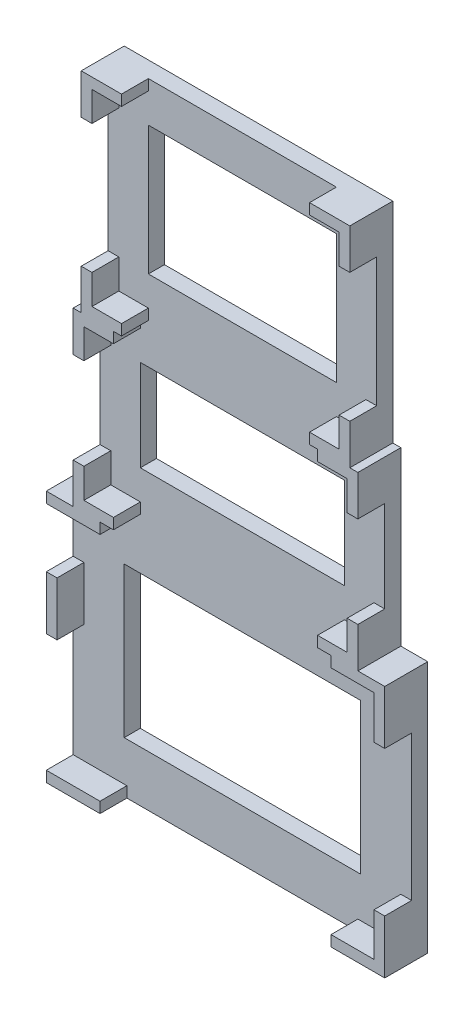
SolidWorks part; units mm, degrees
ref_plane "Front Plane" through (0, 0, 0) normal (0, 0, 1) x (1, 0, 0)
ref_plane "Top Plane" through (0, 0, 0) normal (0, 1, 0) x (1, 0, 0)
ref_plane "Right Plane" through (0, 0, 0) normal (1, 0, 0) x (0, 0, -1)
sketch "Sketch1" plane through (0, 0, 0) normal (0, 0, 1) x (1, 0, 0)
  line L0 (0, 47) -> (5, 47)
  line L1 (0, 0) -> (63, 0)
  line L2 (0, 0) -> (0, 47)
  line L3 (0, 47) -> (63, 47)
  line L4 (63, 0) -> (63, 47)
  line L5 (63, 47) -> (58, 47)
  line L6 (5, 79) -> (6.5, 79)
  line L7 (5, 47) -> (58, 47)
  line L8 (5, 47) -> (5, 79)
  line L9 (5, 79) -> (58, 79)
  line L10 (58, 47) -> (58, 79)
  line L11 (58, 79) -> (56.5, 79)
  line L13 (6.5, 79) -> (56.5, 79)
  line L14 (6.5, 79) -> (6.5, 118)
  line L15 (6.5, 118) -> (56.5, 118)
  line L16 (56.5, 79) -> (56.5, 118)
  dimension "D1" = 63
  dimension "D2" = 47
  dimension "D3" = 5
  dimension "D4" = 5
  dimension "D5" = 32
  dimension "D6" = 1.5
  dimension "D7" = 1.5
  dimension "D8" = 39
extrude "Boss-Extrude1" add sketch "Sketch1" along normal blind 3 contours L1 L4 L3 L0 L2 | L3 L10 L9 L6 L8 | L9 L16 L15 L14
sketch "Sketch2" plane through (0, 0, 3) normal (0, 0, 1) x (1, 0, 0)
  line L0 (0, 47) -> (0, 34)
  line L1 (0, 0) -> (0, 47) construction
  line L2 (0, 34) -> (0, 24)
  line L3 (0, 24) -> (2, 24)
  line L4 (2, 24) -> (2, 34)
  line L5 (2, 34) -> (0, 34)
  line L7 (0, 47) -> (10, 47)
  line L8 (0, 47) -> (0, 45)
  line L9 (0, 45) -> (10, 45)
  line L10 (10, 47) -> (10, 45)
  line L11 (0, 0) -> (10, 0)
  line L12 (0, 0) -> (0, 2)
  line L13 (0, 2) -> (10, 2)
  line L14 (10, 0) -> (10, 2)
  line L15 (63, 0) -> (53, 0)
  line L16 (63, 0) -> (63, 2)
  line L17 (63, 2) -> (53, 2)
  line L18 (53, 0) -> (53, 2)
  line L19 (63, 0) -> (61, 0)
  line L20 (63, 0) -> (63, 10)
  line L21 (63, 10) -> (61, 10)
  line L22 (61, 0) -> (61, 10)
  line L23 (63, 47) -> (53, 47)
  line L24 (63, 47) -> (63, 45)
  line L25 (63, 45) -> (53, 45)
  line L26 (53, 47) -> (53, 45)
  line L27 (63, 47) -> (61, 47)
  line L28 (63, 47) -> (63, 37)
  line L29 (63, 37) -> (61, 37)
  line L30 (61, 47) -> (61, 37)
  line M6 (0, 0) -> (63, 0)
  line M7 (63, 0) -> (63, 47)
  line M8 (63, 47) -> (58, 47)
  line M17 (0, 47) -> (0, 0)
  dimension "D1" = 13
  dimension "D2" = 10
  dimension "D3" = 2
  dimension "D4" = 10
  dimension "D5" = 2
  dimension "D6" = 10
  dimension "D7" = 2
  dimension "D8" = 10
  dimension "D9" = 10
  dimension "D10" = 2
  dimension "D11" = 2
  dimension "D12" = 10
  dimension "D13" = 2
  dimension "D14" = 2
  dimension "D15" = 10
extrude "Boss-Extrude2" add sketch "Sketch2" along normal blind 5 contours L30 L23 L26 L25 | L30 L25 M8 M7 | L25 L30 L29 M7 | L22 L17 L21 M7 | L22 L15 L17 M7 | L22 L17 L18 M6 | L14 L13 M6 M17 | L7 L10 L9 L8 | L2 L3 L4 L5
sketch "Sketch3" plane through (0, 0, 3) normal (0, 0, 1) x (1, 0, 0)
  line L0 (9.5, 45) -> (9.5, 37.5)
  line L1 (10, 2) -> (10, 9.5)
  line L2 (61, 37) -> (53.5, 37)
  line L3 (2, 24) -> (9.5, 24)
  line L4 (0, 45) -> (10, 45) construction
  line L6 (9.5, 37.5) -> (53.5, 37.5)
  line L7 (9.5, 37.5) -> (9.5, 9.5)
  line L8 (9.5, 9.5) -> (53.5, 9.5)
  line L9 (53.5, 37.5) -> (53.5, 9.5)
  dimension "D1" = 7.5
  dimension "D2" = 7.5
  dimension "D3" = 7.5
  dimension "D4" = 7.5
extrude "Cut-Extrude1" cut sketch "Sketch3" against normal blind 5 contours L9 L6 L7 L8
sketch "Sketch4" plane through (0, 0, 3) normal (0, 0, 1) x (1, 0, 0)
  line L0 (63, 47) -> (53, 47) construction
  line L1 (5, 47) -> (12.5, 47)
  line L2 (5, 47) -> (5, 49)
  line L3 (5, 49) -> (12.5, 49)
  line L4 (12.5, 47) -> (12.5, 49)
  line L5 (5, 47) -> (7, 47)
  line L6 (5, 47) -> (5, 54.5)
  line L7 (5, 54.5) -> (7, 54.5)
  line L8 (7, 47) -> (7, 54.5)
  line L9 (58, 47) -> (50.5, 47)
  line L10 (58, 47) -> (58, 49)
  line L11 (58, 49) -> (50.5, 49)
  line L12 (50.5, 47) -> (50.5, 49)
  line L14 (58, 47) -> (56, 47)
  line L15 (58, 47) -> (58, 54.5)
  line L16 (58, 54.5) -> (56, 54.5)
  line L17 (56, 47) -> (56, 54.5)
  line L18 (58, 79) -> (56, 79)
  line L19 (58, 79) -> (58, 71.5)
  line L20 (58, 71.5) -> (56, 71.5)
  line L21 (56, 79) -> (56, 71.5)
  line L22 (58, 79) -> (50.5, 79)
  line L23 (58, 79) -> (58, 77)
  line L24 (58, 77) -> (50.5, 77)
  line L25 (50.5, 79) -> (50.5, 77)
  line L26 (5, 79) -> (12.5, 79)
  line L27 (5, 79) -> (5, 77)
  line L28 (5, 77) -> (12.5, 77)
  line L29 (12.5, 79) -> (12.5, 77)
  line L30 (5, 79) -> (7, 79)
  line L31 (5, 79) -> (5, 71.5)
  line L32 (5, 71.5) -> (7, 71.5)
  line L33 (7, 79) -> (7, 71.5)
  line M20 (53, 47) -> (58, 47)
  line M21 (58, 47) -> (58, 79)
  line M22 (58, 79) -> (56.5, 79)
  line M26 (6.5, 79) -> (5, 79)
  line M27 (5, 79) -> (5, 47)
  line M28 (5, 47) -> (10, 47)
  dimension "D1" = 7.5
  dimension "D2" = 2
  dimension "D3" = 7.5
  dimension "D4" = 2
  dimension "D5" = 2
  dimension "D6" = 7.5
  dimension "D7" = 2
  dimension "D8" = 7.5
  dimension "D9" = 2
  dimension "D10" = 7.5
  dimension "D11" = 2
  dimension "D12" = 7.5
  dimension "D13" = 2
  dimension "D14" = 2
  dimension "D15" = 7.5
  dimension "D16" = 7.5
extrude "Boss-Extrude3" add sketch "Sketch4" along normal blind 5 contours L8 L3 M28 M27 | L3 L8 L7 M27 | L8 L1 L4 L3 | L33 L28 L32 M27 | L33 L26 L28 M26 M27 | L26 L33 L28 L29 | L22 L25 L24 L21 | L24 L19 L18 L21 M22 | L24 L21 L20 M21 | L17 L11 L16 M21 | L17 L9 L11 M21 | L17 L11 L12 L9 M20
sketch "Sketch5" plane through (0, 0, 3) normal (0, 0, 1) x (1, 0, 0)
  line L1 (6.5, 79) -> (14, 79)
  line L2 (6.5, 79) -> (6.5, 81)
  line L3 (6.5, 81) -> (14, 81)
  line L4 (14, 79) -> (14, 81)
  line L5 (6.5, 79) -> (8.5, 79)
  line L6 (6.5, 79) -> (6.5, 86.5)
  line L7 (6.5, 86.5) -> (8.5, 86.5)
  line L8 (8.5, 79) -> (8.5, 86.5)
  line L9 (56.5, 79) -> (49, 79)
  line L10 (56.5, 79) -> (56.5, 81)
  line L11 (56.5, 81) -> (49, 81)
  line L12 (49, 79) -> (49, 81)
  line L13 (56.5, 79) -> (56.5175, 79)
  line L14 (56.5, 79) -> (56.5, 86.5)
  line L17 (56.5, 79) -> (54.5, 79)
  line L18 (56.5, 79) -> (56.5, 86.5)
  line L19 (56.5, 86.5) -> (54.5, 86.5)
  line L20 (54.5, 79) -> (54.5, 86.5)
  line L22 (6.5, 118) -> (8.5, 118)
  line L23 (6.5, 118) -> (6.5, 110.5)
  line L24 (6.5, 110.5) -> (8.5, 110.5)
  line L25 (8.5, 118) -> (8.5, 110.5)
  line L26 (6.5, 118) -> (14, 118)
  line L27 (6.5, 118) -> (6.5, 116)
  line L28 (6.5, 116) -> (14, 116)
  line L29 (14, 118) -> (14, 116)
  line L30 (56.5, 118) -> (49, 118)
  line L31 (56.5, 118) -> (56.5, 116)
  line L32 (56.5, 116) -> (49, 116)
  line L33 (49, 118) -> (49, 116)
  line L34 (56.5, 118) -> (54.5, 118)
  line L35 (56.5, 118) -> (56.5, 110.5)
  line L36 (56.5, 110.5) -> (54.5, 110.5)
  line L37 (54.5, 118) -> (54.5, 110.5)
  line M27 (50.5, 79) -> (56.5, 79)
  line M28 (56.5, 79) -> (56.5, 118)
  line M29 (56.5, 118) -> (6.5, 118)
  line M30 (6.5, 118) -> (6.5, 79)
  line M31 (6.5, 79) -> (12.5, 79)
  dimension "D1" = 7.5
  dimension "D2" = 2
  dimension "D3" = 2
  dimension "D4" = 7.5
  dimension "D5" = 2
  dimension "D6" = 7.5
  dimension "D7" = 7.5
  dimension "D8" = 2
  dimension "D9" = 7.5
  dimension "D10" = 7.5
  dimension "D11" = 2
  dimension "D12" = 2
  dimension "D13" = 2
  dimension "D14" = 2
  dimension "D15" = 7.5
  dimension "D16" = 7.5
extrude "Boss-Extrude4" add sketch "Sketch5" along normal blind 5 contours L3 L8 L7 M30 | L8 L1 L4 L3 | L8 L3 M31 M30 | L20 L11 L12 L9 M27 | L20 L9 L11 M28 | L20 L11 L19 M28 | L37 L30 L33 L32 | L37 L32 M29 M28 | L32 L37 L36 M28 | L29 L25 L28 M29 | L28 L25 M30 M29 | L28 L23 L24 L25
sketch "Sketch6" plane through (0, 0, 3) normal (0, 0, 1) x (1, 0, 0)
  line L0 (12.5, 77) -> (12.5, 71.5)
  line L1 (7, 71.5) -> (12.5, 71.5)
  line L2 (50.5, 49) -> (50.5, 54.5)
  line L4 (12.5, 71.5) -> (50.5, 71.5)
  line L5 (12.5, 71.5) -> (12.5, 54.5)
  line L6 (12.5, 54.5) -> (50.5, 54.5)
  line L7 (50.5, 71.5) -> (50.5, 54.5)
  line L8 (12.5, 71.5) -> (50.5, 71.5)
  line L9 (12.5, 71.5) -> (12.5, 54.5)
  line L10 (12.5, 54.5) -> (50.5, 54.5)
  line L11 (50.5, 71.5) -> (50.5, 54.5)
  dimension "D1" = 5.5
  dimension "D2" = 5.5
extrude "Cut-Extrude2" cut sketch "Sketch6" against normal blind 5 contours L7 L4 L5 L6
sketch "Sketch7" plane through (0, 0, 3) normal (0, 0, 1) x (1, 0, 0)
  line L0 (14, 116) -> (14, 110.5)
  line L1 (49, 81) -> (49, 86.5)
  line L3 (14, 110.5) -> (49, 110.5)
  line L4 (14, 110.5) -> (14, 86.5)
  line L5 (14, 86.5) -> (49, 86.5)
  line L6 (49, 110.5) -> (49, 86.5)
  dimension "D1" = 5.5
  dimension "D2" = 5.5
extrude "Cut-Extrude3" cut sketch "Sketch7" against normal blind 5 contours L6 L3 L4 L5
